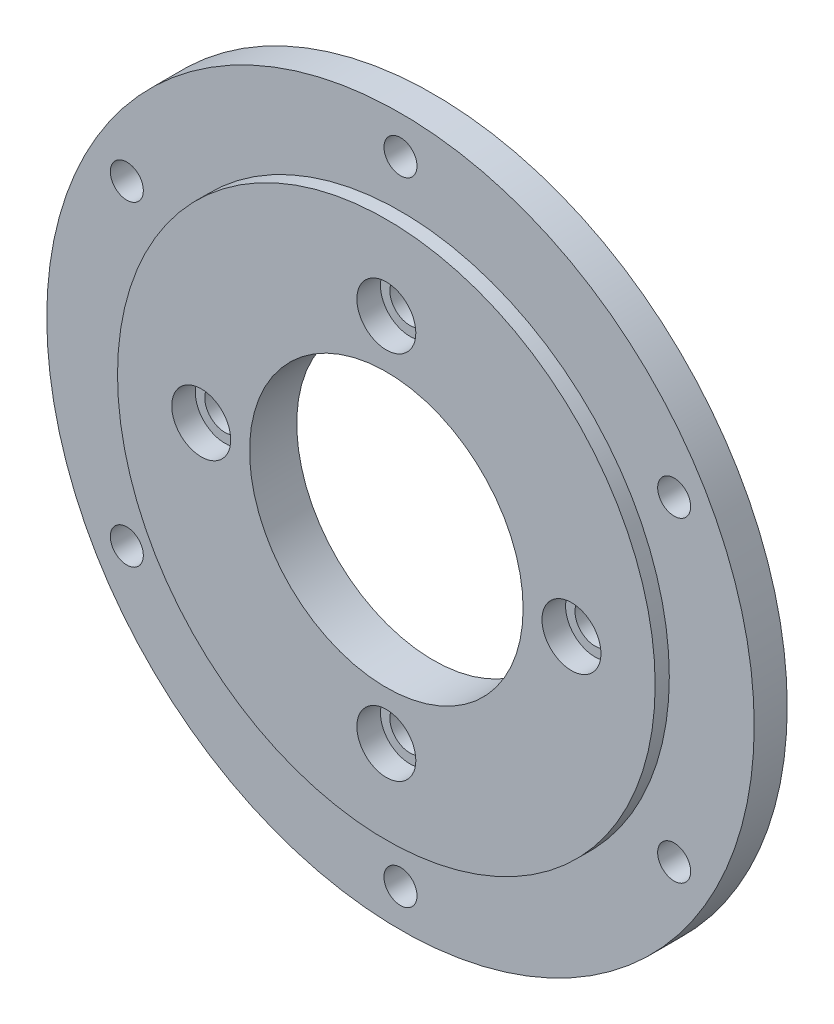
SolidWorks part; units mm, degrees
ref_plane "Front Plane" through (0, 0, 0) normal (0, 0, 1) x (1, 0, 0)
ref_plane "Top Plane" through (0, 0, 0) normal (0, 1, 0) x (1, 0, 0)
ref_plane "Right Plane" through (0, 0, 0) normal (1, 0, 0) x (0, 0, -1)
sketch "Sketch1" plane through (0, 0, 0) normal (0, 0, 1) x (1, 0, 0)
  circle A0 centre (0, 0) radius 75
  circle A1 centre (0, 0) radius 29
  dimension "D1" = 150
  dimension "D2" = 58
extrude "Boss-Extrude1" add sketch "Sketch1" along normal blind 10
sketch "Sketch2" plane through (0, 0, 10) normal (0, 0, 1) x (1, 0, 0)
  circle A0 centre (0, 0) radius 57
  circle A1 centre (0, 0) radius 84.503
  dimension "D1" = 114
extrude "Cut-Extrude2" cut sketch "Sketch2" against normal blind 3
sketch "Sketch3" plane through (0, 0, 10) normal (0, 0, 1) x (1, 0, 0)
  circle A0 centre (0, 39.25) radius 6.25
  circle A3 centre (0, 67) radius 4
  dimension "D3" = 8
  dimension "D4" = 12.5
hole_wizard "Hole1" positions "3DSketch1" profile "Sketch5" legacy end condition through all
sketch3d "3DSketch1"
  point P0 (0, 39.25, 10)
sketch "Sketch5" plane through (0, 39.25, 10) normal (1, 0, 0) x (0, -1, 0)
  line L0 (0, 0) -> (0, 10)
  line L1 (0, 10) -> (4.25, 10)
  line L2 (4.25, 10) -> (4.25, 5)
  line L3 (4.25, 5) -> (6.25, 5)
  line L4 (6.25, 5) -> (6.25, 0)
  line L5 (6.25, 0) -> (0, 0)
  line L6 (0, 110) -> (0, -10) construction
  dimension "Diameter" = 8.5
  dimension "Depth" = 10
  dimension "C-Bore Diameter" = 12.5
  dimension "C-Bore Depth" = 5
pattern_circular "CirPattern1" count 4 every 90 about axis through (0, 0, 0) along (0, 0, 1) of "Hole1"
hole_wizard "Hole2" positions "Sketch6" profile "Sketch7" legacy end condition through all
sketch "Sketch6" plane through (0, 0, 7) normal (0, 0, 1) x (1, 0, 0)
  point P0 (0, 67)
sketch "Sketch7" plane through (0, 67, 7) normal (1, 0, 0) x (0, -1, 0)
  line L0 (0, 0) -> (0, 7)
  line L1 (0, 7) -> (3.5, 7)
  line L2 (3.5, 7) -> (3.5, 0)
  line L3 (3.5, 0) -> (0, 0)
  line L4 (0, 110) -> (0, -10) construction
  dimension "Diameter" = 7
  dimension "Depth" = 7
pattern_circular "CirPattern2" count 6 every 60 about axis through (0, 0, 0) along (0, 0, 1) of "Hole2"
